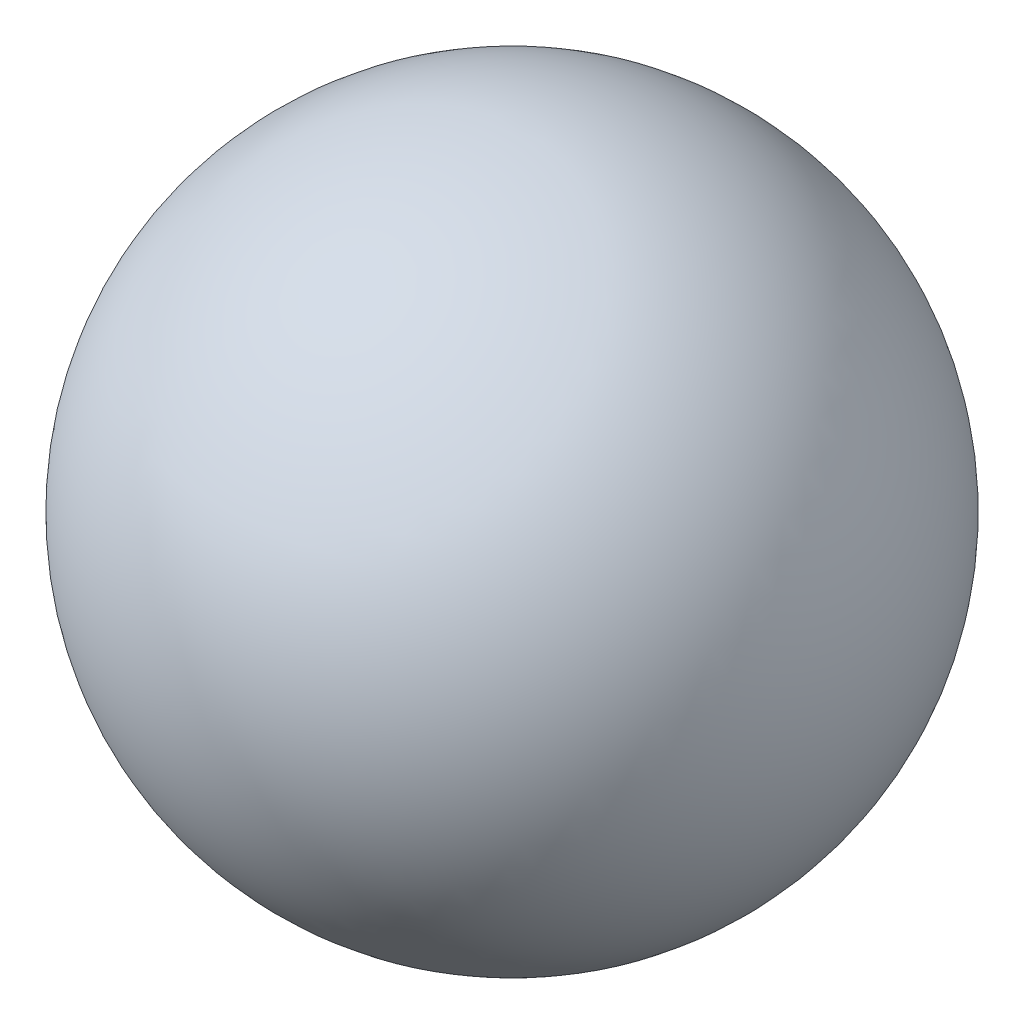
SolidWorks part; units mm, degrees
ref_plane "Front Plane" through (0, 0, 0) normal (0, 0, 1) x (1, 0, 0)
ref_plane "Top Plane" through (0, 0, 0) normal (0, 1, 0) x (1, 0, 0)
ref_plane "Right Plane" through (0, 0, 0) normal (1, 0, 0) x (0, 0, -1)
sketch "Sketch1" plane through (0, 0, 0) normal (0, 0, 1) x (1, 0, 0)
  line L0 (0, 0.5) -> (0, -0.5)
  arc A0 (0, -0.5) -> (0, 0.5) centre (0, 0) ccw
revolve "Revolve1" add sketch "Sketch1" angle 360 about L0
